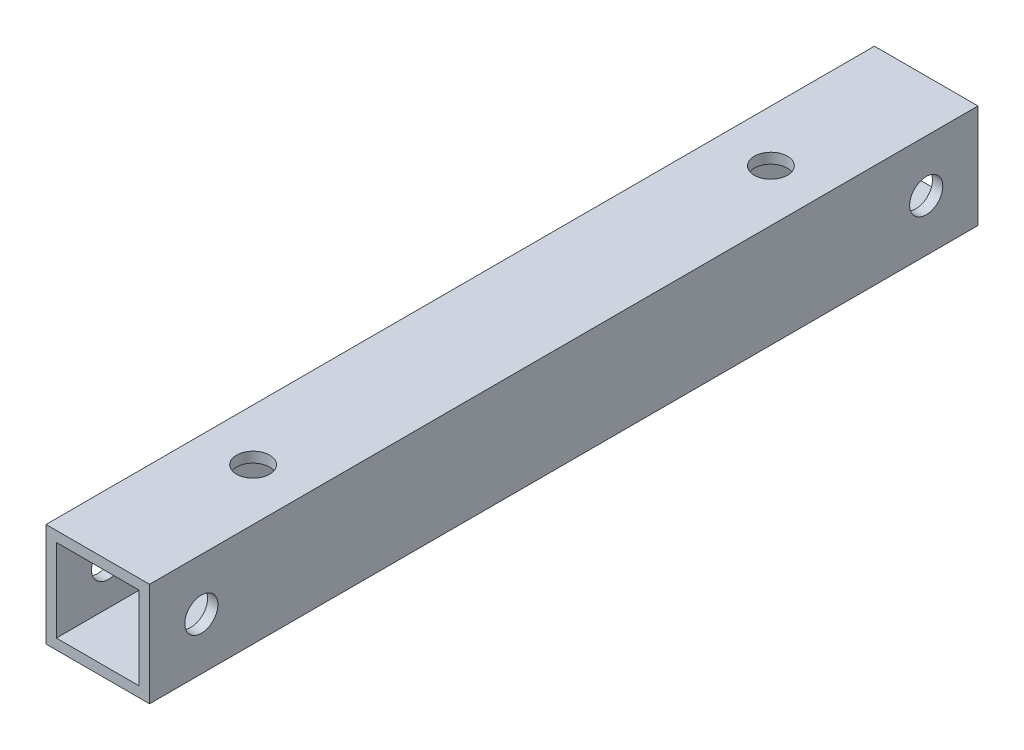
SolidWorks part; units mm, degrees
ref_plane "正面" through (0, 0, 0) normal (0, 0, 1) x (1, 0, 0)
ref_plane "平面" through (0, 0, 0) normal (0, 1, 0) x (1, 0, 0)
ref_plane "右側面" through (0, 0, 0) normal (1, 0, 0) x (0, 0, -1)
sketch "ｽｹｯﾁ1" plane through (0, 0, 0) normal (0, 0, 1) x (1, 0, 0)
  line L1 (0, 0) -> (10, 0)
  line L2 (0, 0) -> (0, 10)
  line L3 (0, 10) -> (10, 10)
  line L4 (10, 0) -> (10, 10)
  line L5 (1, 1) -> (9, 1)
  line L6 (1, 1) -> (1, 9)
  line L7 (1, 9) -> (9, 9)
  line L8 (9, 1) -> (9, 9)
  point P9 (0, 0)
extrude "ﾎﾞｽ - 押し出し1" add sketch "ｽｹｯﾁ1" along normal blind 40
sketch "ｽｹｯﾁ2" plane through (10, 0, 0) normal (1, 0, 0) x (0, 0, -1)
  line L0 (0, 0) -> (0, 10) construction
  circle A0 centre (-5, 5) radius 1.6
  dimension "D1" = 5
extrude "ｶｯﾄ - 押し出し1" cut sketch "ｽｹｯﾁ2" against normal through all
sketch "ｽｹｯﾁ3" plane through (0, 10, 0) normal (0, 1, 0) x (1, 0, 0)
  line L0 (0, -40) -> (0, 0) construction
  line L1 (10, 0) -> (0, 0) construction
  circle A0 centre (5, -15) radius 1.6
  dimension "D1" = 5
  dimension "D2" = 15
extrude "ｶｯﾄ - 押し出し2" cut sketch "ｽｹｯﾁ3" against normal through all
mirror "ﾐﾗｰ1" about plane through (0, 0, 40) normal (0, 0, -1) of bodies 103
